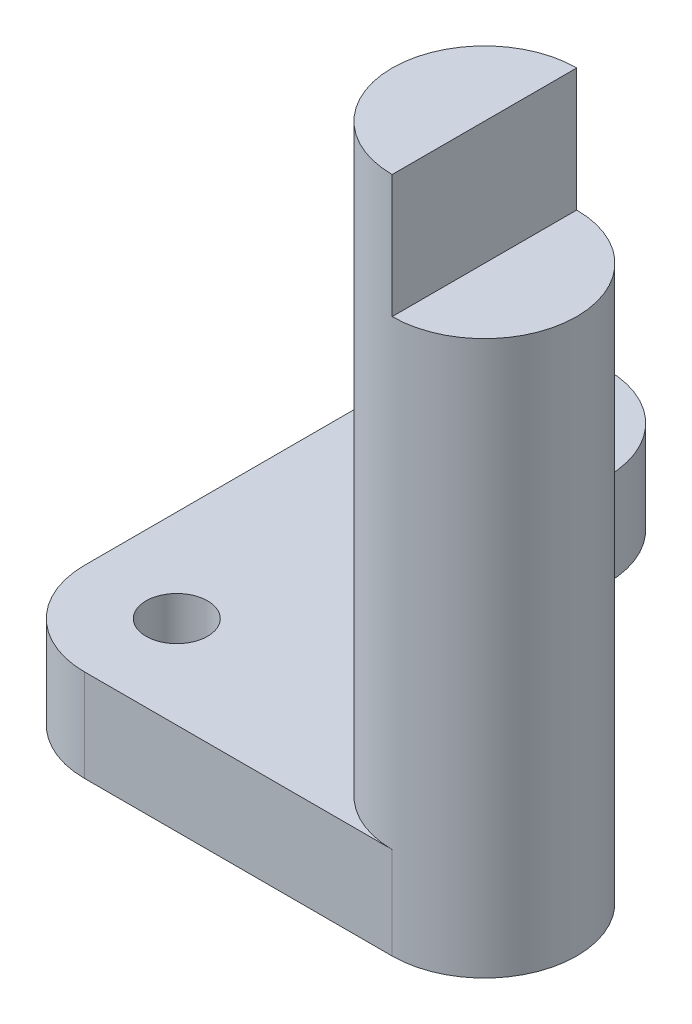
SolidWorks part; units mm, degrees
ref_plane "Front Plane" through (0, 0, 0) normal (0, 0, 1) x (1, 0, 0)
ref_plane "Top Plane" through (0, 0, 0) normal (0, 1, 0) x (1, 0, 0)
ref_plane "Right Plane" through (0, 0, 0) normal (1, 0, 0) x (0, 0, -1)
sketch "Sketch1" plane through (0, 0, 0) normal (0, 1, 0) x (1, 0, 0)
  line L0 (5, -1) -> (1.5, -1)
  line L2 (-1.5, 2.5) -> (-1.5, -2.5)
  line L4 (1.5, 2.5) -> (1.5, -1)
  line L5 (-1.5, 2.5) -> (1.5, -2.5) construction
  line L6 (-1.5, -2.5) -> (1.5, 2.5) construction
  line L7 (5, -4) -> (0, -4)
  line L8 (5, -1) -> (0, -4) construction
  line L9 (0, -1) -> (5, -4) construction
  line L10 (0, -2.5) -> (1.5, -2.5) construction
  line L11 (0, -2.5) -> (0, -4) construction
  line L12 (-0.5, 3) -> (-0.5, 2)
  line L13 (0.5, 3) -> (0.5, 2)
  line L14 (-1.5, 2.5) -> (-1.5, 3)
  line L15 (1.5, 3) -> (1.5, 2.5)
  arc A1 (-1.5, -2.5) -> (0, -4) centre (0, -2.5) ccw
  circle A2 centre (0, -2.5) radius 0.5
  arc A4 (5, -4) -> (5, -1) centre (5, -2.5) ccw
  arc A8 (0.5, 3) -> (-0.5, 3) centre (0, 3) ccw
  arc A9 (-0.5, 2) -> (0.5, 2) centre (0, 2) ccw
  arc A10 (1.5, 3) -> (-1.5, 3) centre (0, 3) ccw
  point P0 (0, 0)
  point P12 (2.5, -2.5)
  dimension "D3" = 1
  dimension "D1" = 3
  dimension "D2" = 5
  dimension "D6" = 90
  dimension "D5" = 2
extrude "Boss-Extrude1" add sketch "Sketch1" along normal blind 1.5
sketch "Sketch2" plane through (0, 1.5, 0) normal (0, 1, 0) x (1, 0, 0)
  circle A0 centre (5, -2.5) radius 1.5
  dimension "D1" = 3
extrude "Boss-Extrude2" add sketch "Sketch2" along normal blind 12
sketch "Sketch3" plane through (0, 13.5, 0) normal (0, 1, 0) x (1, 0, 0)
  line L0 (1.5, -1) -> (5, -1)
  line L1 (5, -4) -> (0, -4)
  line L2 (-1.5, -2.5) -> (-1.5, 2.5)
  line L3 (1.5, 2.5) -> (1.5, -1)
  line L4 (-0.5, 3) -> (-0.5, 2)
  line L5 (0.5, 3) -> (0.5, 2)
  line L6 (-1.5, 3) -> (-1.5, 2.5)
  line L7 (1.5, 3) -> (1.5, 2.5)
  arc A0 (5, -1) -> (5, -4) centre (5, -2.5) cw
  arc A1 (0, -4) -> (-1.5, -2.5) centre (0, -2.5) cw
  circle A4 centre (0, -2.5) radius 0.5
  arc A5 (0.5, 3) -> (-0.5, 3) centre (0, 3) ccw
  arc A6 (-0.5, 2) -> (0.5, 2) centre (0, 2) ccw
  arc A7 (1.5, 3) -> (-1.5, 3) centre (0, 3) ccw
extrude "Boss-Extrude3" add sketch "Sketch3" along normal blind 1.5
sketch "Sketch6" plane through (0, 15, 0) normal (0, 1, 0) x (1, 0, 0)
  line L1 (-3.952, 5.1094) -> (7.2369, 5.1094)
  line L2 (-3.952, 5.1094) -> (-3.952, -4.6639)
  line L3 (-3.952, -4.6639) -> (7.2369, -4.6639)
  line L4 (7.2369, 5.1094) -> (7.2369, -4.6639)
extrude "Cut-Extrude4" cut sketch "Sketch6" against normal blind 6
sketch "Sketch7" plane through (0, 9, 0) normal (0, 1, 0) x (1, 0, 0)
  line L0 (5, -1) -> (5, -4)
  arc A0 (5, -1) -> (5, -4) centre (5, -2.5) ccw
  circle A1 centre (5, -2.5) radius 1.5 construction
  arc A2 (5, -1) -> (5, -4) centre (5, -2.5) ccw construction
extrude "Boss-Extrude4" add sketch "Sketch7" along normal blind 2
